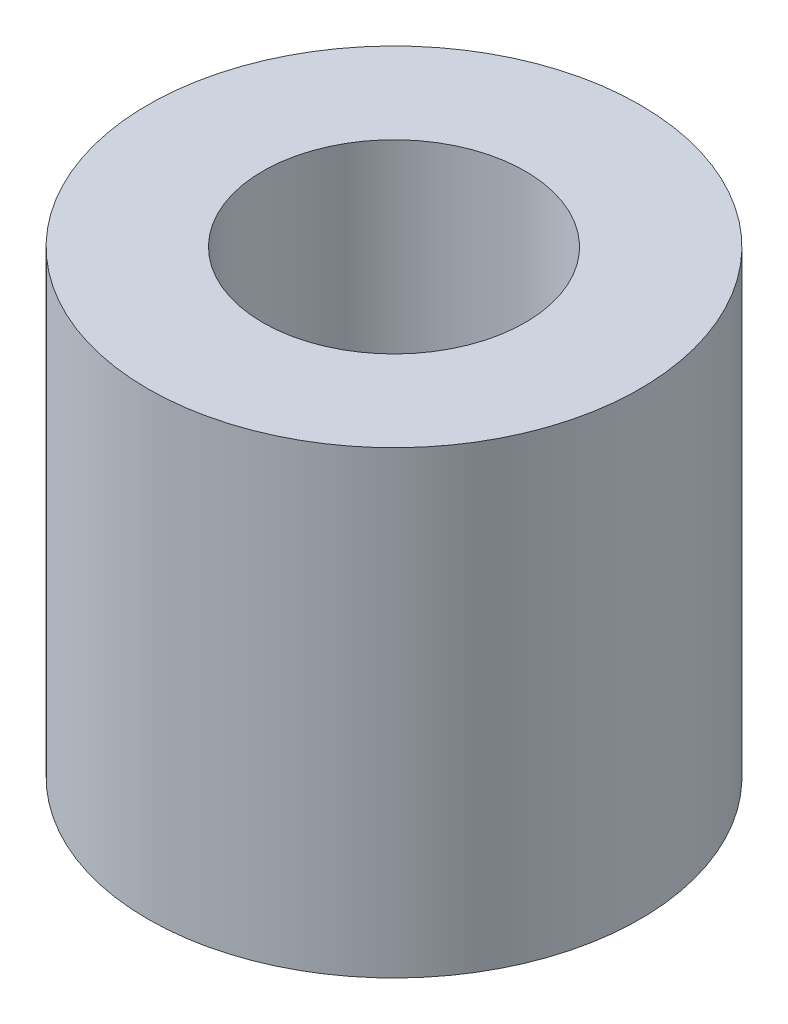
SolidWorks part; units mm, degrees
ref_plane "Front Plane" through (0, 0, 0) normal (0, 0, 1) x (1, 0, 0)
ref_plane "Top Plane" through (0, 0, 0) normal (0, 1, 0) x (1, 0, 0)
ref_plane "Right Plane" through (0, 0, 0) normal (1, 0, 0) x (0, 0, -1)
sketch "Sketch1" plane through (0, 0, 0) normal (0, 0, 1) x (1, 0, 0)
  line L0 (0, 19.51) -> (0, -4.1704) construction
  line L1 (0, 0) -> (-7.5, 0)
  line L2 (-7.5, 0) -> (-7.5, 14)
  line L3 (-7.5, 14) -> (-4, 14)
  line L4 (-4, 14) -> (-4, 4)
  line L5 (-4, 4) -> (0, 1.6906)
  line L6 (-4, 4) -> (0, 4) construction
  line L7 (-4, 14) -> (0, 14) construction
  line L8 (0, 1.6906) -> (0, 0)
  dimension "D1" = 14
  dimension "D2" = 10
  dimension "D3" = 7.5
  dimension "D4" = 4
  dimension "D5" = 60
revolve "Revolve1" add sketch "Sketch1" angle 360 about L0
